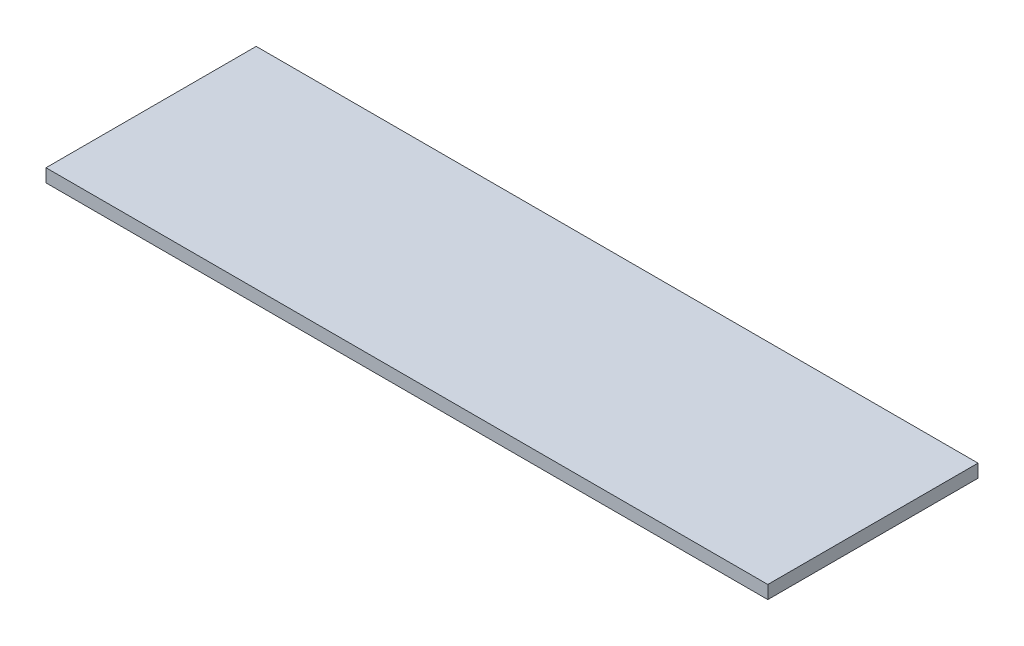
SolidWorks part; units mm, degrees
ref_plane "Front Plane" through (0, 0, 0) normal (0, 0, 1) x (1, 0, 0)
ref_plane "Top Plane" through (0, 0, 0) normal (0, 1, 0) x (1, 0, 0)
ref_plane "Right Plane" through (0, 0, 0) normal (1, 0, 0) x (0, 0, -1)
sketch "Sketch1" plane through (0, 0, 0) normal (0, 1, 0) x (1, 0, 0)
  line L1 (494.5, -144) -> (-494.5, -144)
  line L2 (494.5, -144) -> (494.5, 144)
  line L3 (494.5, 144) -> (-494.5, 144)
  line L4 (-494.5, -144) -> (-494.5, 144)
  line L5 (494.5, -144) -> (-494.5, 144) construction
  line L6 (494.5, 144) -> (-494.5, -144) construction
  point P0 (0, 0)
  dimension "D1" = 288
  dimension "D2" = 989
extrude "Boss-Extrude1" add sketch "Sketch1" along normal blind 18
equation "\"H_DSP\"=18"
equation "\"D1@Boss-Extrude1\"=\"H_DSP\""
